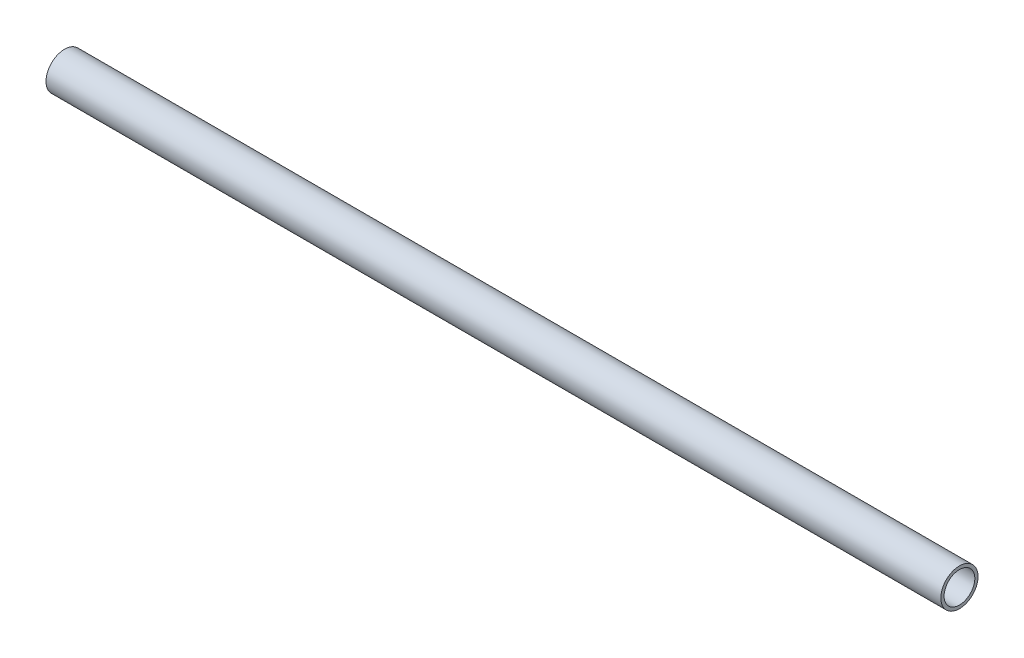
SolidWorks part; units mm, degrees
ref_plane "Front Plane" through (0, 0, 0) normal (0, 0, 1) x (1, 0, 0)
ref_plane "Top Plane" through (0, 0, 0) normal (0, 1, 0) x (1, 0, 0)
ref_plane "Right Plane" through (0, 0, 0) normal (1, 0, 0) x (0, 0, -1)
sketch "Sketch2" plane through (0, 0, 0) normal (0, 1, 0) x (1, 0, 0)
  line L0 (-228.6, 0) -> (228.6, 0)
  line L1 (228.6, -9.4958) -> (-228.6, -9.4958)
  line L2 (228.6, -9.4958) -> (228.6, 9.4958)
  line L3 (228.6, 9.4958) -> (-228.6, 9.4958)
  line L4 (-228.6, -9.4958) -> (-228.6, 9.4958)
  line L5 (228.6, -9.4958) -> (-228.6, 9.4958) construction
  line L6 (228.6, 9.4958) -> (-228.6, -9.4958) construction
  line L7 (-231.4283, 9.4958) -> (-231.4283, -9.4958) construction
  line L8 (228.6, -7.8448) -> (-228.6, -7.8448)
  line L9 (228.6, -7.8448) -> (228.6, 7.8448)
  line L10 (228.6, 7.8448) -> (-228.6, 7.8448)
  line L11 (-228.6, -7.8448) -> (-228.6, 7.8448)
  line L12 (228.6, -7.8448) -> (-228.6, 7.8448) construction
  line L13 (228.6, 7.8448) -> (-228.6, -7.8448) construction
  line L14 (-231.4283, 9.4958) -> (225.7717, 9.4958) construction
  point P0 (0, 0)
  point P9 (0, 0)
  dimension "D1" = 1.651
revolve "Revolve1" add sketch "Sketch2" angle 360 about L0
